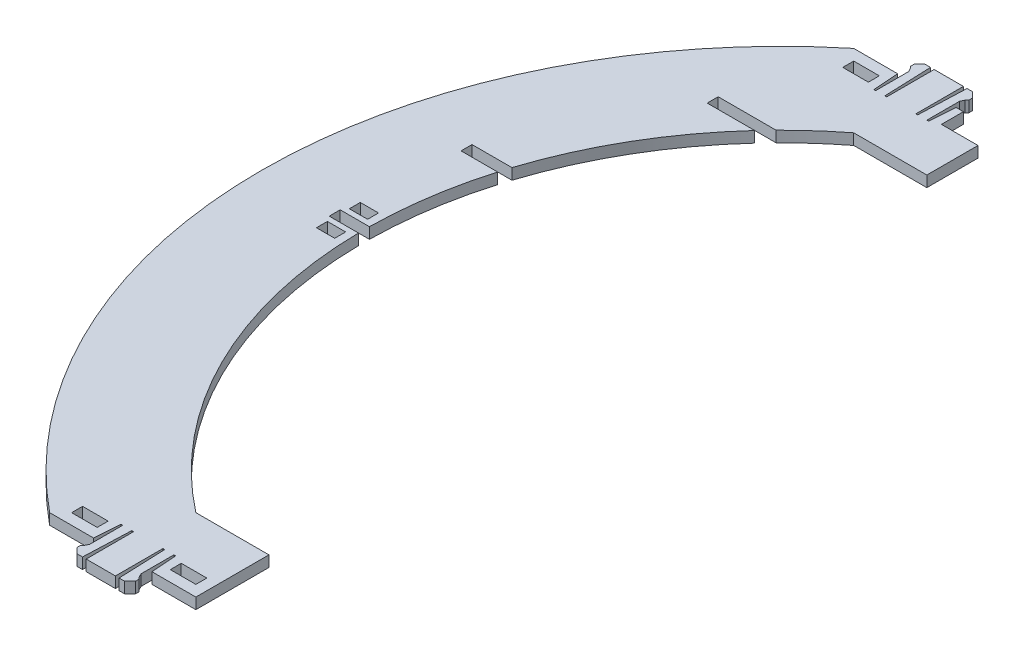
SolidWorks part; units mm, degrees
ref_plane "Front Plane" through (0, 0, 0) normal (0, 0, 1) x (1, 0, 0)
ref_plane "Top Plane" through (0, 0, 0) normal (0, 1, 0) x (1, 0, 0)
ref_plane "Right Plane" through (0, 0, 0) normal (1, 0, 0) x (0, 0, -1)
sketch "Sketch2" plane through (0, 0, 0) normal (0, 1, 0) x (1, 0, 0)
  line L0 (-70, 90) -> (-50, 90)
  line L1 (-50, 90) -> (-50, 110)
  line L2 (-50, 110) -> (-61.9955, 110)
  line L3 (-90, 110) -> (-77.9955, 110)
  line L4 (-77.9955, 110) -> (-77.4955, 102.9978)
  line L5 (-50, -90) -> (-50, -110)
  line L6 (-70, -90) -> (-50, -90)
  line L7 (-77.4955, 102.9978) -> (-76.9955, 102.9978)
  line L8 (-76.9955, 102.9978) -> (-76.9955, 111.9978)
  line L9 (-76.9955, 111.9978) -> (-77.4955, 112.9978)
  line L10 (-77.4955, 112.9978) -> (-77.9955, 113.4978)
  line L11 (-77.9955, 113.4978) -> (-77.9955, 114.4978)
  line L12 (-77.9955, 114.4978) -> (-76.4955, 115.9978)
  line L13 (-76.4955, 115.9978) -> (-74.9955, 115.9978)
  line L14 (-74.9955, 115.9978) -> (-74.4955, 102.9978)
  line L15 (-74.4955, 102.9978) -> (-73.9955, 102.9978)
  line L16 (-73.9955, 102.9978) -> (-73.9955, 115.9978)
  line L17 (-69.9955, 110) -> (-69.9955, 115.7386) construction
  line L18 (-65.9955, 102.9978) -> (-65.9955, 115.9978)
  line L19 (-65.4955, 102.9978) -> (-65.9955, 102.9978)
  line L20 (-64.9955, 115.9978) -> (-65.4955, 102.9978)
  line L21 (-63.4955, 115.9978) -> (-64.9955, 115.9978)
  line L22 (-61.9955, 114.4978) -> (-63.4955, 115.9978)
  line L23 (-61.9955, 113.4978) -> (-61.9955, 114.4978)
  line L24 (-62.4955, 112.9978) -> (-61.9955, 113.4978)
  line L25 (-62.9955, 111.9978) -> (-62.4955, 112.9978)
  line L26 (-62.9955, 102.9978) -> (-62.9955, 111.9978)
  line L27 (-62.4955, 102.9978) -> (-62.9955, 102.9978)
  line L28 (-61.9955, 110) -> (-62.4955, 102.9978)
  line L29 (-73.9955, 115.9978) -> (-65.9955, 115.9978)
  line L31 (-90, -110) -> (-78.0045, -110)
  line L32 (-62.0045, -110) -> (-50, -110)
  line L33 (-62.0045, -110) -> (-62.5045, -102.9978)
  line L34 (-62.5045, -102.9978) -> (-63.0045, -102.9978)
  line L35 (-63.0045, -102.9978) -> (-63.0045, -111.9978)
  line L36 (-63.0045, -111.9978) -> (-62.5045, -112.9978)
  line L37 (-62.5045, -112.9978) -> (-62.0045, -113.4978)
  line L38 (-62.0045, -113.4978) -> (-62.0045, -114.4978)
  line L39 (-62.0045, -114.4978) -> (-63.5045, -115.9978)
  line L40 (-63.5045, -115.9978) -> (-65.0045, -115.9978)
  line L41 (-65.0045, -115.9978) -> (-65.5045, -102.9978)
  line L42 (-65.5045, -102.9978) -> (-66.0045, -102.9978)
  line L43 (-66.0045, -102.9978) -> (-66.0045, -115.9978)
  line L44 (-70.0045, -110) -> (-70.0045, -115.7386) construction
  line L45 (-74.0045, -102.9978) -> (-74.0045, -115.9978)
  line L46 (-74.5045, -102.9978) -> (-74.0045, -102.9978)
  line L47 (-75.0045, -115.9978) -> (-74.5045, -102.9978)
  line L48 (-76.5045, -115.9978) -> (-75.0045, -115.9978)
  line L49 (-78.0045, -114.4978) -> (-76.5045, -115.9978)
  line L50 (-78.0045, -113.4978) -> (-78.0045, -114.4978)
  line L51 (-77.5045, -112.9978) -> (-78.0045, -113.4978)
  line L52 (-77.0045, -111.9978) -> (-77.5045, -112.9978)
  line L53 (-77.0045, -102.9978) -> (-77.0045, -111.9978)
  line L54 (-77.5045, -102.9978) -> (-77.0045, -102.9978)
  line L55 (-78.0045, -110) -> (-77.5045, -102.9978)
  line L56 (-66.0045, -115.9978) -> (-74.0045, -115.9978)
  line L57 (-74.0045, -115.9978) -> (-74.0543, -115.8666)
  arc A0 (-70, -90) -> (-70, 90) centre (0, 0) cw
  arc A1 (-90, -110) -> (-90, 110) centre (0, 0) cw
  point P18 (-69.9955, 110)
  point P19 (-77.9955, 110)
  point P20 (-61.9955, 110)
  point P21 (-61.9955, 110)
  point P50 (-70.0045, -110)
  point P51 (-62.0045, -110)
  point P52 (-78.0045, -110)
  point P53 (-78.0045, -110)
  dimension "D8" = 142.1267
  dimension "D1" = 50
  dimension "D2" = 90
  dimension "D4" = 20
  dimension "D5" = 20
  dimension "D6" = 90
  dimension "D7" = 20
  dimension "D9" = 70
  dimension "D10" = 20
  dimension "D11" = 11.9955
  dimension "D12" = 7.0022
  dimension "D13" = 8
  dimension "D14" = 0.5
  dimension "D15" = 12.0045
  dimension "D16" = 0.5
  dimension "D17" = 9
  dimension "D18" = 0.5
  dimension "D19" = 1
  dimension "D20" = 0.5
  dimension "D21" = 0.5
  dimension "D22" = 1
  dimension "D23" = 1.5
  dimension "D24" = 1.5
  dimension "D25" = 1.5
  dimension "D26" = 0.5
  dimension "D27" = 13
  dimension "D28" = 0.5
  dimension "D29" = 13
  dimension "D30" = 11.9955
  dimension "D31" = 8
  dimension "D32" = 8
  dimension "D33" = 7.02
  dimension "D34" = 0.5
  dimension "D35" = 0.5
  dimension "D36" = 9
  dimension "D37" = 0.5
  dimension "D38" = 1
  dimension "D39" = 0.5
  dimension "D40" = 0.5
  dimension "D41" = 1
  dimension "D42" = 1.5
  dimension "D43" = 1.5
  dimension "D44" = 1.5
  dimension "D45" = 0.5
  dimension "D46" = 13
  dimension "D47" = 0.5
  dimension "D48" = 13
  dimension "D49" = 12.0045
  dimension "D50" = 8
extrude "Boss-Extrude2" add sketch "Sketch2" along normal blind 3 contours L56 L43 L42 L41 L40 L39 L38 L37 L36 L35 L34 L33 L32 L5 L6 A0 L0 L1 L2 L28 L27 L26 L25 L24 L23 L22 L21 L20 L19 L18 L29 L16 L15 L14 L13 L12 L11 L10 L9 L8 L7 L4 L3 A1 L31 L55 L54 L53 L52 L51 L50 L49 L48 L47 L46 L45
sketch "Sketch3" plane through (0, 3, 0) normal (0, 1, 0) x (1, 0, 0)
  line L1 (-60, 110) -> (-50, 110)
  line L2 (-60, 110) -> (-60, 104)
  line L3 (-60, 104) -> (-50, 104)
  line L4 (-50, 110) -> (-50, 104)
  line L5 (-87, 107) -> (-80, 107)
  line L6 (-87, 107) -> (-87, 104)
  line L7 (-87, 104) -> (-80, 104)
  line L8 (-80, 107) -> (-80, 104)
  line L9 (-59.9911, -104) -> (-52.9911, -104)
  line L10 (-59.9911, -104) -> (-59.9911, -107)
  line L11 (-59.9911, -107) -> (-52.9911, -107)
  line L12 (-52.9911, -104) -> (-52.9911, -107)
  line L13 (-86.9911, -104) -> (-79.9911, -104)
  line L14 (-86.9911, -104) -> (-86.9911, -107)
  line L15 (-86.9911, -107) -> (-79.9911, -107)
  line L16 (-79.9911, -104) -> (-79.9911, -107)
  line L22 (-90, -110) -> (-78.0045, -110) construction
  line L23 (-62.0045, -110) -> (-50, -110) construction
  line L25 (-90, 110) -> (-77.9955, 110) construction
  line L26 (-50, 110) -> (-61.9955, 110) construction
  dimension "D1" = 6
  dimension "D2" = 3
  dimension "D3" = 10.0045
  dimension "D4" = 9.9955
  dimension "D5" = 0
  dimension "D6" = 10
  dimension "D7" = 3
  dimension "D8" = 7
  dimension "D9" = 3
  dimension "D10" = 7
  dimension "D11" = 3
  dimension "D12" = 7
  dimension "D13" = 3
  dimension "D14" = 3
  dimension "D15" = 10.0045
  dimension "D16" = 9.9955
extrude "Cut-Extrude1" cut sketch "Sketch3" against normal blind 3 contours L13 L16 L15 L14 | L9 L12 L11 L10 | L7 L8 L5 L6 | L3 L4 L1 L2
sketch "Sketch8" plane through (0, 3, 0) normal (0, 1, 0) x (1, 0, 0)
  line L0 (-114.0077, 1.5) -> (-122.0077, 1.5)
  line L1 (-122.0077, 1.5) -> (-122.0077, -1.5)
  line L2 (-122.0077, -1.5) -> (-114.0077, -1.5)
  arc A0 (-70, 90) -> (-70, -90) centre (0, 0) ccw construction
  dimension "D1" = 8
  dimension "D2" = 3
  dimension "D3" = 8
sketch "Sketch9" plane through (0, 3, 0) normal (0, 1, 0) x (1, 0, 0)
  line L3 (-81.2404, 80) -> (-97.0892, 80)
  line L4 (-97.0892, 80) -> (-97.0892, 77)
  line L5 (-97.0892, 77) -> (-84.0892, 77)
  line L6 (-60, 110) -> (-61.9955, 110) construction
  arc A0 (-70, 90) -> (-70, -90) centre (0, 0) ccw construction
  point P14 (-60.9978, 110)
  dimension "D3" = 3
  dimension "D4" = 30
  dimension "D5" = 13
extrude "Cut-Extrude3" cut sketch "Sketch8" against normal blind 3 and the other way through all contours L0 L1 L2
sketch "Sketch10" plane through (0, 3, 0) normal (0, 1, 0) x (1, 0, 0)
  line L0 (0, -46.5479) -> (0, 46.5479) construction
  line L2 (-122.0077, 0) -> (-126.0574, 0) construction
  line L3 (-121.0077, 6) -> (-116.0077, 6)
  line L4 (-121.0077, 6) -> (-121.0077, 3)
  line L5 (-121.0077, 3) -> (-116.0077, 3)
  line L6 (-116.0077, 6) -> (-116.0077, 3)
  line L7 (-122.0077, -1.5) -> (-122.0077, 1.5) construction
  line L8 (-122.0077, 1.5) -> (-114.0077, 1.5) construction
  line L9 (-116.0077, -6) -> (-116.0077, -3)
  line L10 (-121.0077, -3) -> (-116.0077, -3)
  line L11 (-121.0077, -6) -> (-121.0077, -3)
  line L12 (-121.0077, -6) -> (-116.0077, -6)
  point P7 (0, 0)
  dimension "D1" = 1.5
  dimension "D2" = 1
  dimension "D3" = 5
  dimension "D4" = 3
extrude "Cut-Extrude4" cut sketch "Sketch10" against normal blind 10 contours L4 L5 L6 L3
extrude "Cut-Extrude12" cut sketch "Sketch9" against normal blind 3 and the other way through all contours L3 L4 L5
sketch "Sketch13" plane through (0, 3, 0) normal (0, 1, 0) x (1, 0, 0)
  line L0 (-108.5127, 35) -> (-119.4349, 35)
  line L1 (-119.4349, 35) -> (-119.4349, 32)
  line L2 (-119.4349, 32) -> (-109.4349, 32)
  line L3 (-60, 110) -> (-61.9955, 110) construction
  arc A0 (-84.0892, 77) -> (-114.0077, 1.5) centre (0, 0) ccw construction
  dimension "D1" = 3
  dimension "D2" = 10
  dimension "D3" = 75
extrude "Cut-Extrude13" cut sketch "Sketch13" against normal blind 3 and the other way through all
sketch "Sketch15" plane through (0, 3, 0) normal (0, 1, 0) x (1, 0, 0)
  text T0 "B2" font "Century Gothic" height in points 22
  dimension "D1" = 91.5
  dimension "D2" = 64.5
